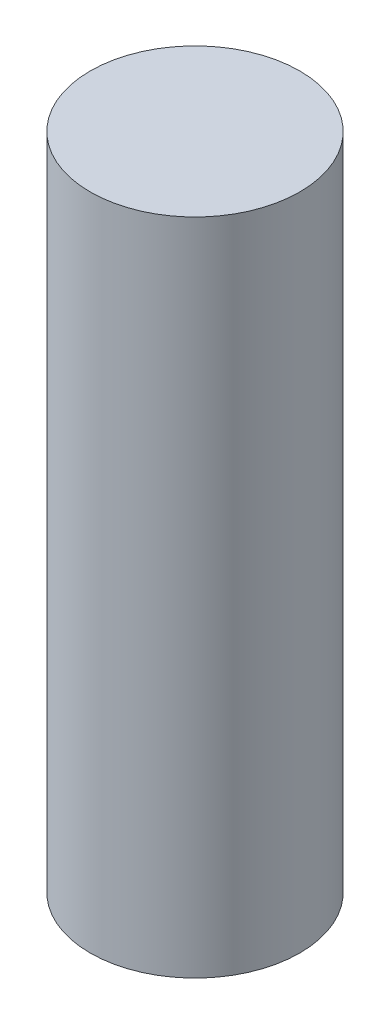
SolidWorks part; units mm, degrees
ref_plane "Front Plane" through (0, 0, 0) normal (0, 0, 1) x (1, 0, 0)
ref_plane "Top Plane" through (0, 0, 0) normal (0, 1, 0) x (1, 0, 0)
ref_plane "Right Plane" through (0, 0, 0) normal (1, 0, 0) x (0, 0, -1)
sketch "Sketch1" plane through (0, 0, 0) normal (0, 1, 0) x (1, 0, 0)
  circle A0 centre (0, 0) radius 1.59
extrude "Boss-Extrude1" add sketch "Sketch1" along normal blind 10 contours A0
